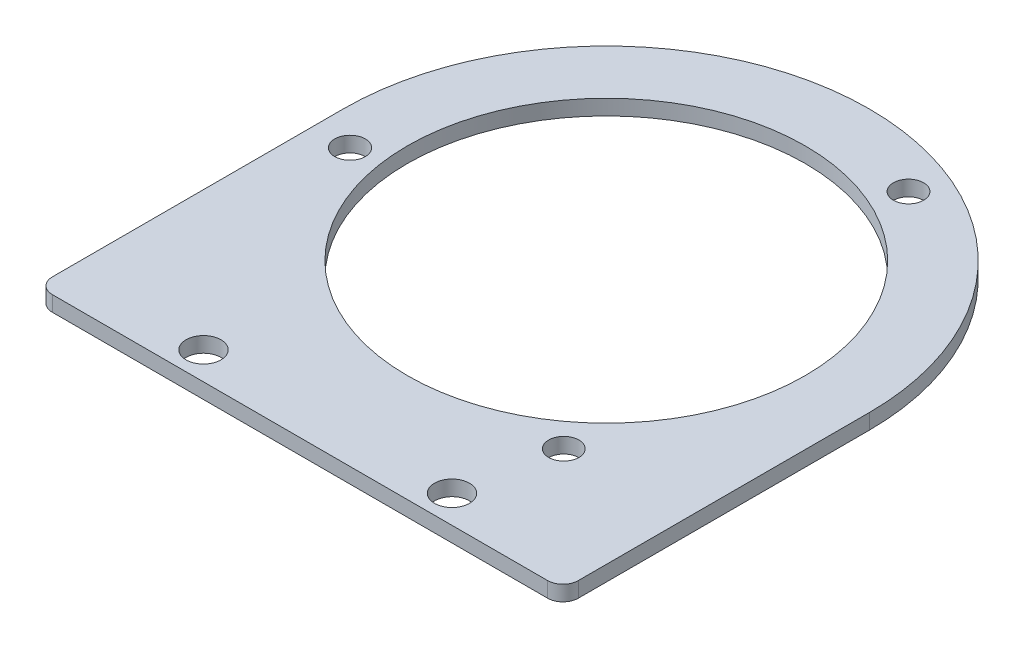
SolidWorks part; units mm, degrees
ref_plane "Front Plane" through (0, 0, 0) normal (0, 0, 1) x (1, 0, 0)
ref_plane "Top Plane" through (0, 0, 0) normal (0, 1, 0) x (1, 0, 0)
ref_plane "Right Plane" through (0, 0, 0) normal (1, 0, 0) x (0, 0, -1)
sketch "Sketch4" plane through (0, 0, 0) normal (0, 1, 0) x (1, 0, 0)
  line L0 (-102.6827, -127) -> (102.6827, -127)
  line L1 (109.0327, -120.65) -> (109.0327, 0)
  line L2 (-109.0327, 0) -> (-109.0327, -120.65)
  line L3 (-51.5149, -115.4874) -> (-51.5149, -127) construction
  line L4 (0, -116.8469) -> (0, -105.3343) construction
  arc A0 (-109.0327, 0) -> (109.0327, 0) centre (0, 0) cw
  circle A1 centre (0, 0) radius 82.4943
  circle A2 centre (-51.5149, -115.4874) radius 7.2466
  circle A3 centre (51.5149, -115.4874) radius 7.2466
  arc A5 (102.6827, -127) -> (109.0327, -120.65) centre (102.6827, -120.65) ccw
  arc A6 (-102.6827, -127) -> (-109.0327, -120.65) centre (-102.6827, -120.65) cw
  circle A8 centre (-93.6824, -12.5611) radius 6.3519
  circle A11 centre (37.8028, 87.5005) radius 6.2835
  circle A12 centre (58.6974, -76.3199) radius 6.2784
  point P19 (-109.0327, -127)
  point P22 (109.0327, -127)
  point P30 (0, 0)
  dimension "D4" = 14.4933
  dimension "D5" = 164.9886
  dimension "D8" = 6.35
  dimension "D1" = 127
  dimension "D2" = 218.0654
  dimension "D3" = 51.5149
  dimension "D6" = 11.5126
extrude "Boss-Extrude1" add sketch "Sketch4" along normal blind 6.35
